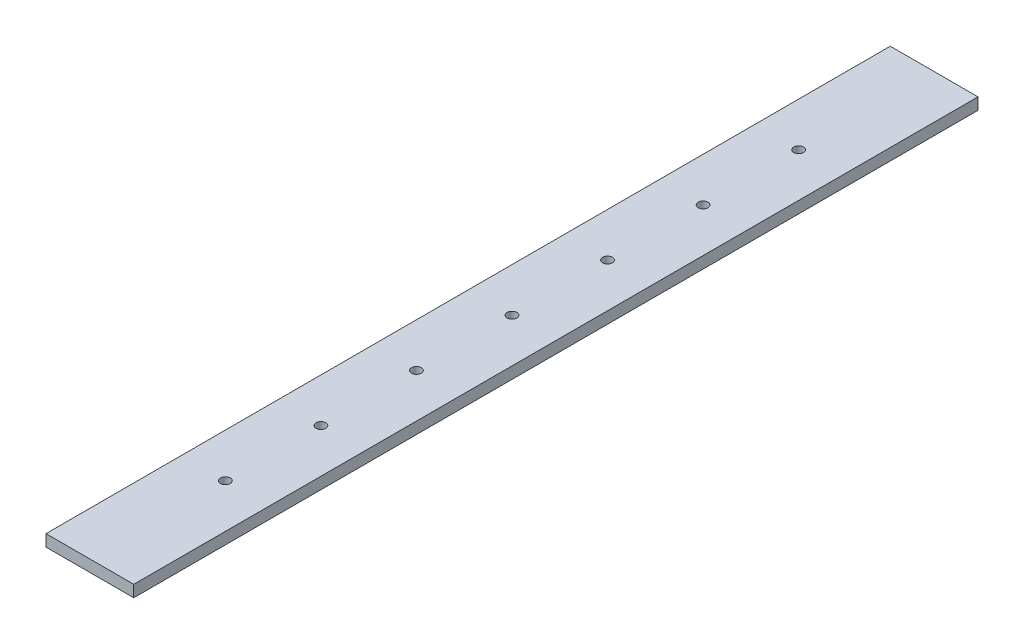
SolidWorks part; units mm, degrees
ref_plane "Front Plane" through (0, 0, 0) normal (0, 0, 1) x (1, 0, 0)
ref_plane "Top Plane" through (0, 0, 0) normal (0, 1, 0) x (1, 0, 0)
ref_plane "Right Plane" through (0, 0, 0) normal (1, 0, 0) x (0, 0, -1)
sketch "Sketch1" plane through (0, 0, 0) normal (0, 1, 0) x (1, 0, 0)
  line L1 (0, 0) -> (285.75, 0)
  line L2 (0, 0) -> (0, -2749.55)
  line L3 (0, -2749.55) -> (285.75, -2749.55)
  line L4 (285.75, 0) -> (285.75, -2749.55)
extrude "Boss-Extrude1" add sketch "Sketch1" along normal blind 38.1
sketch "Sketch3" plane through (0, 38.1, 0) normal (0, 1, 0) x (1, 0, 0)
  line L0 (142.875, -2749.55) -> (142.875, -2463.8) construction
  line L1 (0, -2749.55) -> (285.75, -2749.55) construction
  line L2 (142.875, -2463.8) -> (142.875, -2308.225) construction
  line L3 (142.875, -2308.225) -> (142.875, -1997.075) construction
  line L4 (142.875, -1997.075) -> (142.875, -1685.925) construction
  line L5 (142.875, -1685.925) -> (142.875, -1374.775) construction
  line L6 (142.875, -1374.775) -> (142.875, -1063.625) construction
  line L7 (142.875, -1063.625) -> (142.875, -752.475) construction
  line L8 (142.875, -752.475) -> (142.875, -441.325) construction
  line L9 (142.875, -441.325) -> (142.875, -285.75) construction
  line L10 (142.875, -285.75) -> (142.875, 0) construction
  circle A1 centre (142.875, -2308.225) radius 15.875
  circle A2 centre (142.875, -1997.075) radius 15.875
  circle A3 centre (142.875, -1685.925) radius 15.875
  circle A4 centre (142.875, -1374.775) radius 15.875
  circle A5 centre (142.875, -1063.625) radius 15.875
  circle A6 centre (142.875, -752.475) radius 15.875
  circle A7 centre (142.875, -441.325) radius 15.875
  point P18 (0, 0)
  point P20 (0, 0)
  point P22 (0, 0)
  point P23 (0, 0)
  point P24 (0, 0)
  point P25 (0, 0)
  point P26 (0, 0)
  point P27 (0, 0)
  point P28 (0, 0)
  point P29 (0, 0)
  point P30 (0, 0)
  point P31 (0, 0)
  point P32 (0, 0)
  point P33 (0, 0)
extrude "Cut-Extrude1" cut sketch "Sketch3" against normal through all
sketch "Sketch6" plane through (0, 0, 2749.55) normal (0, 0, 1) x (1, 0, 0)
  line L0 (142.875, 38.1) -> (142.875, 0)
  line L1 (0, 38.1) -> (285.75, 38.1) construction
  line L2 (0, 0) -> (285.75, 0) construction
sketch "Sketch8" plane through (0, 0, 0) normal (0, 0, -1) x (-1, 0, 0)
  line L0 (-142.875, 38.1) -> (-142.875, 0)
  line L1 (-285.75, 38.1) -> (0, 38.1) construction
  line L2 (-285.75, 0) -> (0, 0) construction
